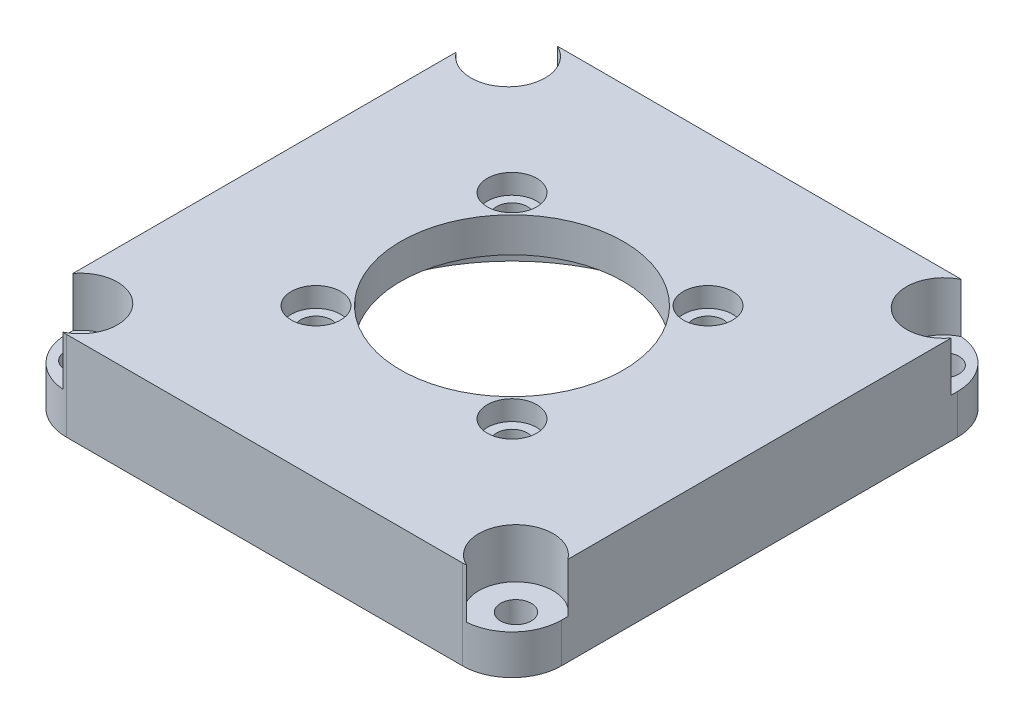
SolidWorks part; units mm, degrees
ref_plane "前视基准面" through (0, 0, 0) normal (0, 0, 1) x (1, 0, 0)
ref_plane "上视基准面" through (0, 0, 0) normal (0, 1, 0) x (1, 0, 0)
ref_plane "右视基准面" through (0, 0, 0) normal (1, 0, 0) x (0, 0, -1)
sketch "Sketch1" plane through (0, 0, 0) normal (0, 1, 0) x (1, 0, 0)
  line L1 (-25, -25) -> (25, -25)
  line L2 (-25, -25) -> (-25, 25)
  line L3 (-25, 25) -> (25, 25)
  line L4 (25, -25) -> (25, 25)
  line L5 (-25, -25) -> (25, 25) construction
  line L6 (-25, 25) -> (25, -25) construction
  point P0 (0, 0)
  dimension "D1" = 50
  dimension "D2" = 50
extrude "Boss-Extrude1" add sketch "Sketch1" along normal blind 12
fillet "Fillet1" radius 5 4 edges at (-25, 6, -25) (-25, 6, 25) (25, 6, 25) (25, 6, -25)
sketch "Sketch3" plane through (0, 0, 0) normal (0, -1, 0) x (1, 0, 0)
  circle A0 centre (0, 0) radius 18.25
  dimension "D1" = 36.5
extrude "Cut-Extrude1" cut sketch "Sketch3" against normal blind 5.5
sketch "Sketch4" plane through (0, 5.5, 0) normal (0, -1, 0) x (1, 0, 0)
  circle A0 centre (0, 0) radius 11.25
  dimension "D1" = 22.5
extrude "Cut-Extrude2" cut sketch "Sketch4" against normal blind 10
sketch "Sketch5" plane through (0, 12, 0) normal (0, 1, 0) x (1, 0, 0)
  line L1 (31.4896, 35.2267) -> (-31.4896, 35.2267)
  line L2 (31.4896, 35.2267) -> (31.4896, -35.2267)
  line L3 (31.4896, -35.2267) -> (-31.4896, -35.2267)
  line L4 (-31.4896, 35.2267) -> (-31.4896, -35.2267)
  line L5 (31.4896, 35.2267) -> (-31.4896, -35.2267) construction
  line L6 (31.4896, -35.2267) -> (-31.4896, 35.2267) construction
  point P0 (0, 0)
extrude "Cut-Extrude3" cut sketch "Sketch5" against normal blind 3
sketch "Sketch6" plane through (0, 9, 0) normal (0, 1, 0) x (1, 0, 0)
  line L0 (0, 0) -> (-23.5355, 23.5355) construction
  line L1 (0, 0) -> (23.5355, -23.5355) construction
  line L2 (23.5355, 23.5355) -> (-23.5355, -23.5355) construction
  arc A0 (-20, 25) -> (-25, 20) centre (-20, 20) ccw construction
  arc A1 (20, -25) -> (25, -20) centre (20, -20) ccw construction
  arc A2 (25, 20) -> (20, 25) centre (20, 20) ccw construction
  arc A3 (-25, -20) -> (-20, -25) centre (-20, -20) ccw construction
  circle A4 centre (-9.8995, 9.8995) radius 2.5
  circle A5 centre (9.8995, 9.8995) radius 2.5
  circle A6 centre (-9.8995, -9.8995) radius 2.5
  circle A7 centre (9.8995, -9.8995) radius 2.5
  dimension "D1" = 5
  dimension "D2" = 28
  dimension "D3" = 14
  dimension "D4" = 28
  dimension "D5" = 14
extrude "Cut-Extrude4" cut sketch "Sketch6" against normal blind 2
sketch "Sketch7" plane through (0, 7, 0) normal (0, 1, 0) x (1, 0, 0)
  circle A0 centre (-9.8995, 9.8995) radius 1.55
  circle A1 centre (9.8995, 9.8995) radius 1.55
  circle A2 centre (-9.8995, -9.8995) radius 1.55
  circle A3 centre (9.8995, -9.8995) radius 1.55
  dimension "D1" = 3.1
extrude "Cut-Extrude5" cut sketch "Sketch7" against normal blind 3
sketch "Sketch8" plane through (0, 9, 0) normal (0, 1, 0) x (1, 0, 0)
  line L0 (-20, 25) -> (20, 25) construction
  line L1 (-25, -20) -> (-25, 20) construction
  circle A0 centre (-22, 21.6) radius 1.55
  dimension "D1" = 3.1
  dimension "D3" = 3
  dimension "D2" = 3.4
extrude "Cut-Extrude6" cut sketch "Sketch8" against normal blind 12
sketch "Sketch9" plane through (0, 9, 0) normal (0, 1, 0) x (1, 0, 0)
  circle A0 centre (-22, 21.6) radius 3.75
  dimension "D1" = 7.5
extrude "Cut-Extrude7" cut sketch "Sketch9" against normal blind 5
mirror "Mirror1" about plane through (0, 0, 0) normal (1, 0, 0) of "Cut-Extrude6", "Cut-Extrude7"
mirror "Mirror2" about plane through (0, 0, 0) normal (0, 0, 1) of "Mirror1", "Cut-Extrude6", "Cut-Extrude7"
